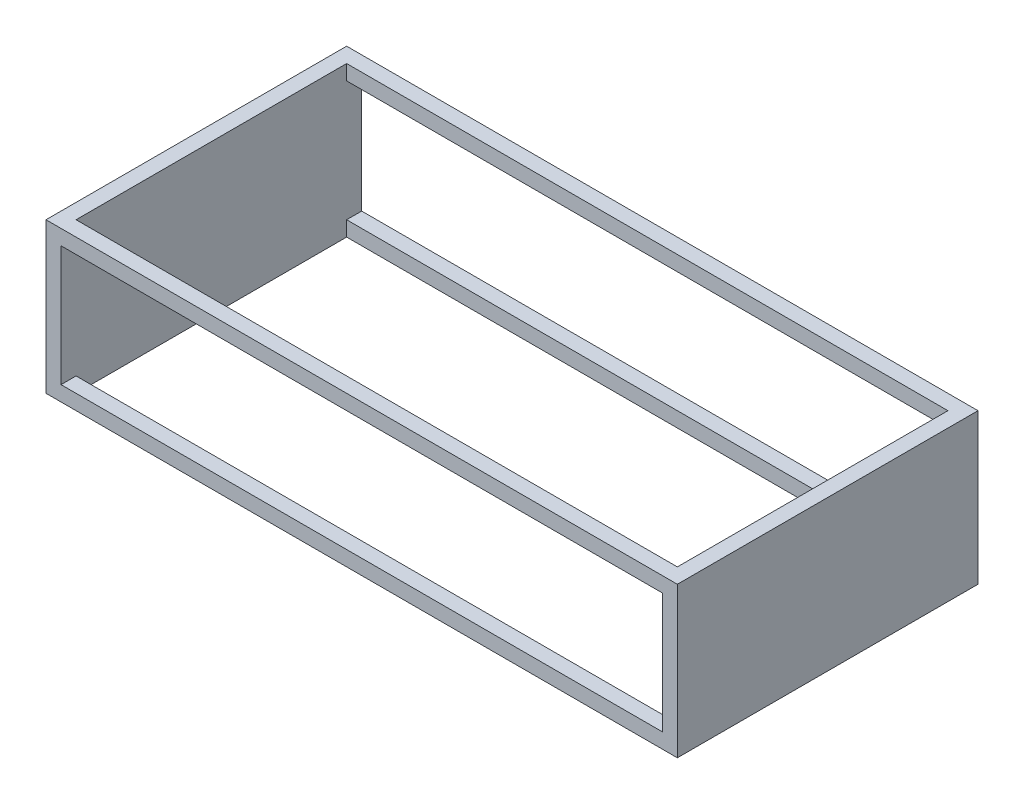
SolidWorks part; units mm, degrees
ref_plane "Front Plane" through (0, 0, 0) normal (0, 0, 1) x (1, 0, 0)
ref_plane "Top Plane" through (0, 0, 0) normal (0, 1, 0) x (1, 0, 0)
ref_plane "Right Plane" through (0, 0, 0) normal (1, 0, 0) x (0, 0, -1)
sketch "Sketch1" plane through (0, 0, 0) normal (0, 1, 0) x (1, 0, 0)
  line L1 (-1050, -500) -> (1050, -500)
  line L2 (-1050, -500) -> (-1050, 500)
  line L3 (-1050, 500) -> (1050, 500)
  line L4 (1050, -500) -> (1050, 500)
  line L5 (-1050, -500) -> (1050, 500) construction
  line L6 (-1050, 500) -> (1050, -500) construction
  point P0 (0, 0)
  dimension "D1" = 2100
  dimension "D2" = 1000
extrude "Boss-Extrude1" add sketch "Sketch1" along normal mid plane 500
sketch "Sketch2" plane through (0, 250, 0) normal (0, 1, 0) x (1, 0, 0)
  line L1 (-1000, -450) -> (1000, -450)
  line L2 (-1000, -450) -> (-1000, 450)
  line L3 (-1000, 450) -> (1000, 450)
  line L4 (1000, -450) -> (1000, 450)
  line L5 (-1000, -450) -> (1000, 450) construction
  line L6 (-1000, 450) -> (1000, -450) construction
  point P0 (0, 0)
  dimension "D1" = 2000
  dimension "D2" = 900
extrude "Cut-Extrude1" cut sketch "Sketch2" against normal up to next
sketch "Sketch3" plane through (0, 0, -500) normal (0, 0, -1) x (-1, 0, 0)
  line L1 (-1000, -200) -> (1000, -200)
  line L2 (-1000, -200) -> (-1000, 200)
  line L3 (-1000, 200) -> (1000, 200)
  line L4 (1000, -200) -> (1000, 200)
  line L5 (-1000, -200) -> (1000, 200) construction
  line L6 (-1000, 200) -> (1000, -200) construction
  point P0 (0, 0)
  dimension "D1" = 400
  dimension "D2" = 2000
extrude "Cut-Extrude2" cut sketch "Sketch3" against normal blind 1206
